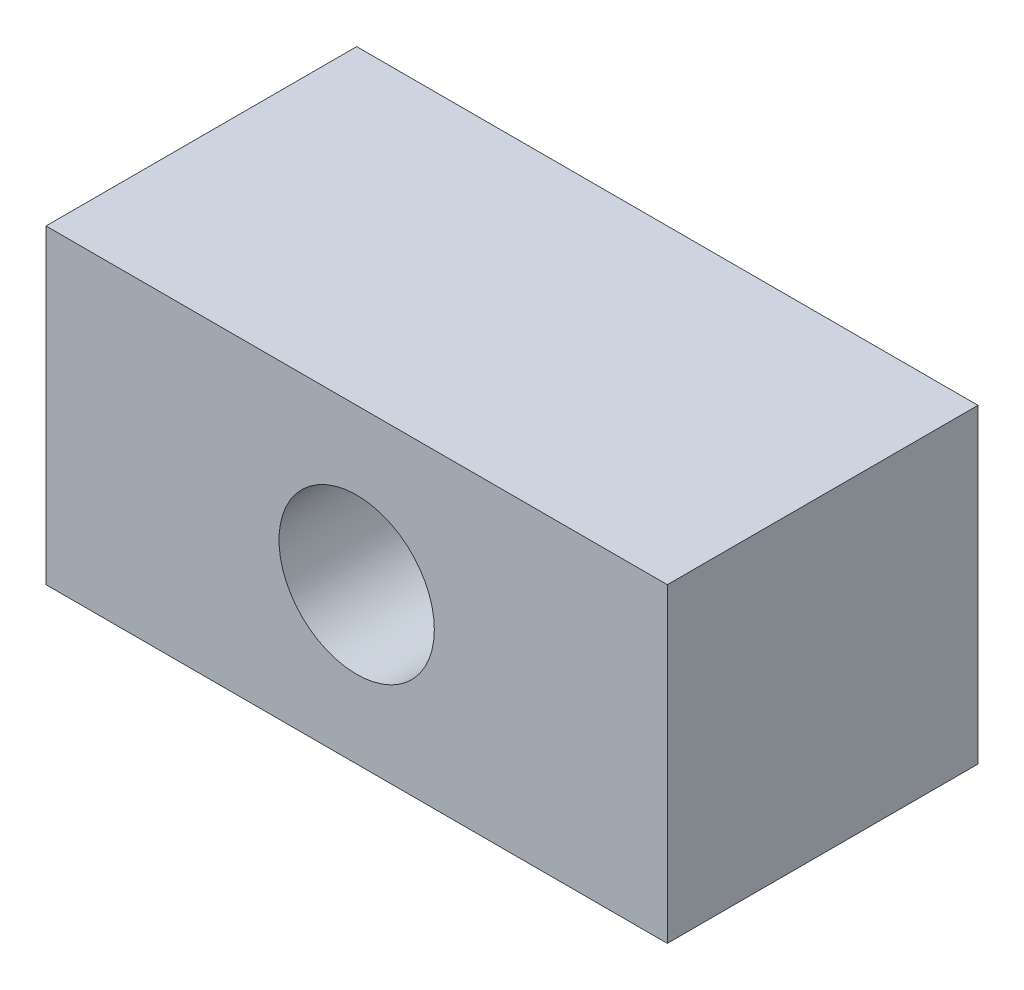
SolidWorks part; units mm, degrees
ref_plane "Front Plane" through (0, 0, 0) normal (0, 0, 1) x (1, 0, 0)
ref_plane "Top Plane" through (0, 0, 0) normal (0, 1, 0) x (1, 0, 0)
ref_plane "Right Plane" through (0, 0, 0) normal (1, 0, 0) x (0, 0, -1)
sketch "Sketch1" plane through (0, 0, 0) normal (0, 0, 1) x (1, 0, 0)
  line L1 (-30, -15) -> (30, -15)
  line L2 (-30, -15) -> (-30, 15)
  line L3 (-30, 15) -> (30, 15)
  line L4 (30, -15) -> (30, 15)
  line L5 (-30, -15) -> (30, 15) construction
  line L6 (-30, 15) -> (30, -15) construction
  circle A0 centre (0, 0) radius 7.5
  point P0 (0, 0)
  dimension "D3" = 15
  dimension "D1" = 60
  dimension "D2" = 30
extrude "Boss-Extrude1" add sketch "Sketch1" along normal blind 30
